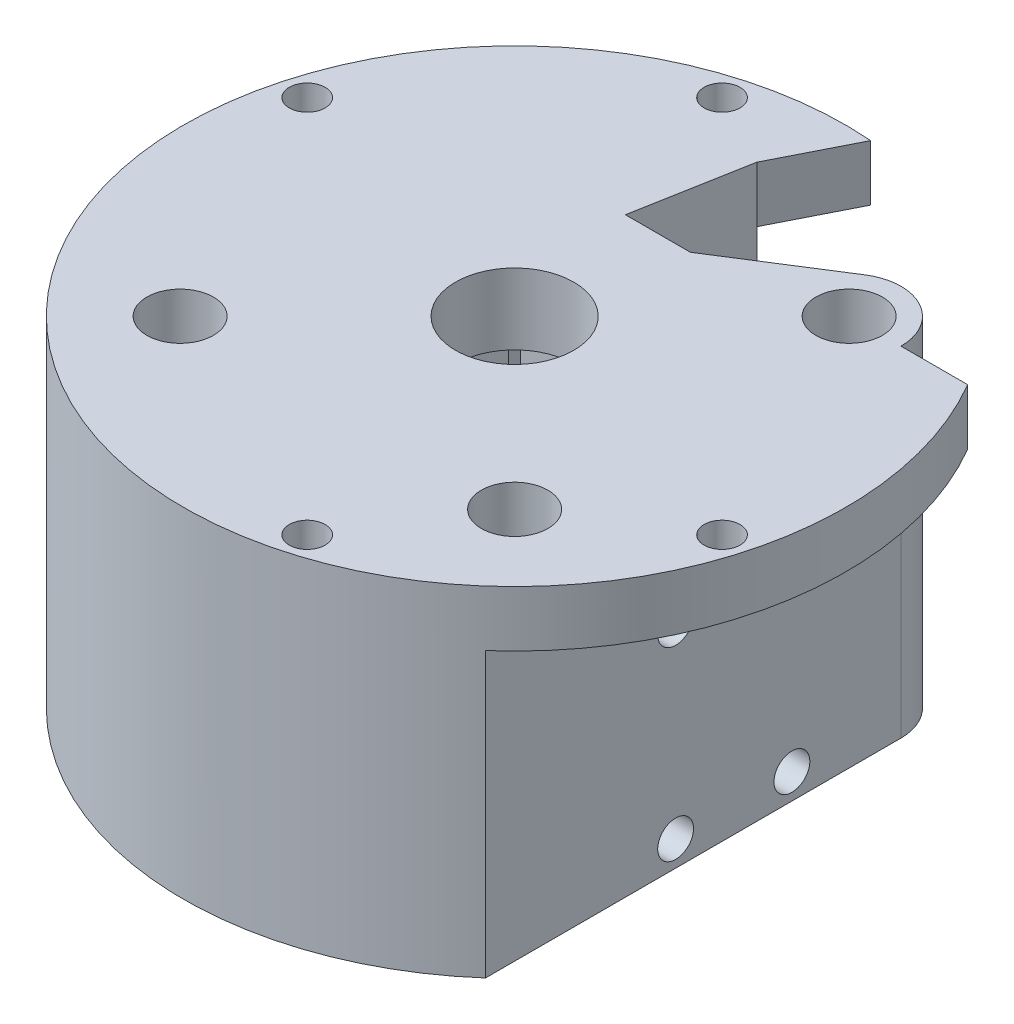
SolidWorks part; units mm, degrees
ref_plane "Front Plane" through (0, 0, 0) normal (0, 0, 1) x (1, 0, 0)
ref_plane "Top Plane" through (0, 0, 0) normal (0, 1, 0) x (1, 0, 0)
ref_plane "Right Plane" through (0, 0, 0) normal (1, 0, 0) x (0, 0, -1)
sketch "Sketch2" plane through (0, 0, 0) normal (0, 1, 0) x (1, 0, 0)
  line L0 (-46.3406, 15.0473) -> (-20.9548, -39.0545) construction
  line L1 (-17.9605, 17.9605) -> (-3.0236, 17.9605) construction
  line L2 (-17.9605, 17.9605) -> (-17.9605, -17.9605) construction
  line L3 (-17.9605, -17.9605) -> (17.9605, -17.9605) construction
  line L4 (17.9605, 17.9605) -> (17.9605, -17.9605) construction
  line L5 (-17.9605, 17.9605) -> (17.9605, -17.9605) construction
  line L6 (-17.9605, -17.9605) -> (17.9605, 17.9605) construction
  line L7 (10.05, -30.05) -> (-10.05, -30.05)
  line L8 (10.05, -30.05) -> (10.05, 10.05)
  line L9 (10.05, 10.05) -> (3.4925, 10.05)
  line L10 (-10.05, -30.05) -> (-10.05, 10.05)
  line L11 (10.05, -30.05) -> (-10.05, 10.05) construction
  line L12 (10.05, 10.05) -> (-10.05, -30.05) construction
  line L13 (-3.4925, 15.384) -> (3.4925, 15.384) construction
  line L14 (-3.4925, 15.384) -> (-3.4925, 10.05)
  line L15 (0, 10.05) -> (3.4925, 10.05) construction
  line L16 (3.4925, 15.384) -> (3.4925, 10.05)
  line L17 (0, 12.717) -> (3.4925, 10.05) construction
  line L18 (0, 12.717) -> (3.4925, 15.384) construction
  line L19 (-1.3182, 27.3309) -> (-10.8398, 32.142)
  line L20 (-1.3182, 27.3309) -> (-23.3118, -16.1961) construction
  line L21 (-23.3118, -16.1961) -> (-32.8333, -11.3851) construction
  line L22 (-10.8398, 32.142) -> (-32.8333, -11.3851) construction
  line L23 (-1.3182, 27.3309) -> (-32.8333, -11.3851) construction
  line L24 (-23.3118, -16.1961) -> (-10.8398, 32.142) construction
  line L25 (23.5324, -17.9605) -> (23.5324, -26.6597)
  line L26 (23.5324, -17.9605) -> (23.5324, 17.9605)
  line L27 (3.4925, 15.384) -> (14.9767, 22.6661)
  line L28 (-10.8398, 32.142) -> (-12.8493, 33.1573)
  line L29 (-3.4925, 15.384) -> (-1.3182, 27.3309)
  line L30 (-3.0236, 17.9605) -> (7.5558, 17.9605) construction
  line L31 (7.5558, 17.9605) -> (17.9605, 17.9605) construction
  line L32 (-3.4925, 15.384) -> (0, 12.717) construction
  line L33 (-3.4925, 10.05) -> (0, 12.717) construction
  line L34 (0, 10.05) -> (-3.4925, 10.05) construction
  line L35 (-3.4925, 10.05) -> (-10.05, 10.05)
  line L36 (-3.4925, 10.05) -> (0, 10.05) construction
  line L37 (3.4925, 10.05) -> (0, 10.05) construction
  arc A0 (-12.8493, 33.1573) -> (23.5324, -26.6597) centre (0, 0) ccw
  circle A1 centre (-17.9605, 17.9605) radius 3.5719 construction
  circle A2 centre (17.9605, 17.9605) radius 3.5719
  circle A3 centre (17.9605, -17.9605) radius 3.5719
  circle A4 centre (-17.9605, -17.9605) radius 3.5719
  arc A5 (-4.4901, 4.4901) -> (4.4901, 4.4901) centre (0, 0) ccw construction
  arc A6 (-7.1064, 7.1064) -> (7.1064, 7.1064) centre (0, 0) ccw construction
  circle A7 centre (-17.9605, -17.9605) radius 5.5719 construction
  arc A8 (23.5324, -17.9605) -> (17.9605, -12.3886) centre (17.9605, -17.9605) ccw construction
  arc A9 (23.5324, 17.9605) -> (14.9767, 22.6661) centre (17.9605, 17.9605) ccw
  arc A10 (23.5324, -26.6597) -> (-12.8493, 33.1573) centre (0, 0) ccw construction
  arc A11 (0, 10.05) -> (-7.1064, 7.1064) centre (0, 0) ccw construction
  arc A12 (4.4901, 4.4901) -> (-4.4901, 4.4901) centre (0, 0) ccw construction
  arc A13 (7.1064, 7.1064) -> (0, 10.05) centre (0, 0) ccw construction
  arc A14 (14.0206, 14.0206) -> (17.9605, 12.3886) centre (17.9605, 17.9605) ccw construction
  arc A15 (12.3886, 17.9605) -> (14.0206, 14.0206) centre (17.9605, 17.9605) ccw construction
  arc A16 (14.9767, 22.6661) -> (12.3886, 17.9605) centre (17.9605, 17.9605) ccw construction
  arc A17 (17.9605, 12.3886) -> (23.5324, 17.9605) centre (17.9605, 17.9605) ccw construction
  arc A18 (12.3886, -17.9605) -> (23.5324, -17.9605) centre (17.9605, -17.9605) ccw construction
  arc A19 (14.0206, -14.0206) -> (12.3886, -17.9605) centre (17.9605, -17.9605) ccw construction
  arc A20 (17.9605, -12.3886) -> (14.0206, -14.0206) centre (17.9605, -17.9605) ccw construction
  point P12 (0, -10)
  point P17 (0, 12.717)
  point P23 (-17.0758, 7.9729)
  point P35 (-32.1922, -15.1054)
  dimension "D1" = 71.12
  dimension "D3" = 7.1437
  dimension "D4" = 12.7
  dimension "D2" = 50.8
  dimension "D5" = 20.1
  dimension "D6" = 40.1
  dimension "D7" = 10
  dimension "D8" = 6.985
  dimension "D9" = 5.334
  dimension "D10" = 10.668
  dimension "D11" = 48.768
  dimension "D12" = 10.668
  dimension "D13" = 2
  dimension "D14" = 1
  dimension "D15" = 38.056
extrude "Boss-Extrude1" add sketch "Sketch2" along normal blind 1.905
sketch "Sketch3" plane through (0, 1.905, 0) normal (0, 1, 0) x (1, 0, 0)
  line L0 (-1.3182, 27.3309) -> (-23.3118, -16.1961) construction
  line L1 (-10.8398, 32.142) -> (-32.8333, -11.3851) construction
  line L2 (-23.3118, -16.1961) -> (-32.8333, -11.3851) construction
  line L3 (-10.8398, 32.142) -> (-32.8333, -11.3851)
  line L4 (-1.3182, 27.3309) -> (-9.7636, 10.6168)
  line L5 (-23.3118, -16.1961) -> (-32.8333, -11.3851)
  line L6 (-10.05, 10.05) -> (-9.415, 10.05) construction
  line L7 (-9.7636, 10.6168) -> (-10.05, 10.05) construction
  line L8 (-10.3364, 9.4832) -> (-23.3118, -16.1961)
  line L9 (-10.05, 10.05) -> (-10.3364, 9.4832) construction
  line L10 (-10.05, 9.415) -> (-10.05, 10.05) construction
  line L11 (-10.05, 10.05) -> (-3.4925, 10.05)
  line L12 (-3.4925, 10.05) -> (-3.4925, 15.384)
  line L13 (-3.4925, 15.384) -> (-1.3182, 27.3309)
  line L14 (-1.3182, 27.3309) -> (-12.8493, 33.1573)
  line L15 (23.5324, -26.6597) -> (23.5324, 17.9605)
  line L16 (14.9767, 22.6661) -> (3.4925, 15.384)
  line L17 (3.4925, 15.384) -> (3.4925, 10.05)
  line L18 (3.4925, 10.05) -> (10.05, 10.05)
  line L19 (10.05, 10.05) -> (10.05, -30.05)
  line L20 (10.05, -30.05) -> (-10.05, -30.05)
  line L21 (-10.05, -30.05) -> (-10.05, 10.05)
  line L22 (-9.415, 10.05) -> (-3.4925, 10.05)
  line L23 (-3.4925, 10.05) -> (-3.4925, 15.384)
  line L24 (-3.4925, 15.384) -> (-1.3182, 27.3309)
  line L25 (-10.8398, 32.142) -> (-12.8493, 33.1573)
  line L26 (23.5324, -26.6597) -> (23.5324, 17.9605)
  line L27 (14.9767, 22.6661) -> (3.4925, 15.384)
  line L28 (3.4925, 15.384) -> (3.4925, 10.05)
  line L29 (3.4925, 10.05) -> (10.05, 10.05)
  line L30 (10.05, 10.05) -> (10.05, -30.05)
  line L31 (10.05, -30.05) -> (-10.05, -30.05)
  line L32 (-10.05, -30.05) -> (-10.05, 9.415)
  line L33 (-1.3182, 27.3309) -> (-10.8398, 32.142) construction
  arc A0 (-10.3364, 9.4832) -> (-10.05, 9.415) centre (-10.05, 10.05) ccw
  circle A1 centre (17.9605, 17.9605) radius 3.5719 construction
  circle A2 centre (17.9605, -17.9605) radius 3.5719 construction
  arc A3 (-12.8493, 33.1573) -> (23.5324, -26.6597) centre (0, 0) ccw
  arc A4 (23.5324, 17.9605) -> (14.9767, 22.6661) centre (17.9605, 17.9605) ccw
  arc A5 (-12.8493, 33.1573) -> (23.5324, -26.6597) centre (0, 0) ccw
  arc A6 (23.5324, 17.9605) -> (14.9767, 22.6661) centre (17.9605, 17.9605) ccw
  circle A7 centre (-17.9605, -17.9605) radius 3.5719 construction
  circle A8 centre (17.9605, 17.9605) radius 3.5719
  circle A9 centre (17.9605, -17.9605) radius 3.5719
  circle A10 centre (-17.9605, -17.9605) radius 3.5719
  arc A11 (-9.7636, 10.6168) -> (-10.3364, 9.4832) centre (-10.05, 10.05) ccw construction
  arc A12 (-10.05, 9.415) -> (-9.415, 10.05) centre (-10.05, 10.05) ccw construction
  arc A13 (-9.415, 10.05) -> (-9.7636, 10.6168) centre (-10.05, 10.05) ccw
  dimension "D1" = 1.27
  dimension "D2" = 0
extrude "Boss-Extrude2" add sketch "Sketch3" along normal blind 19.558
sketch "Sketch4" plane through (0, 21.463, 0) normal (0, 1, 0) x (1, 0, 0)
  line L0 (0, 10.05) -> (3.4925, 10.05) construction
  line L1 (-3.4925, 15.384) -> (3.4925, 15.384) construction
  line L2 (0, 10.05) -> (-3.4925, 10.05) construction
  line L3 (0, 10.05) -> (-3.4925, 10.05)
  line L4 (0, 10.05) -> (3.4925, 10.05)
  line L5 (-3.4925, 15.384) -> (3.4925, 15.384)
  line L6 (-23.3118, -16.1961) -> (-32.8333, -11.3851) construction
  line L7 (-10.8398, 32.142) -> (-32.8333, -11.3851) construction
  line L8 (-1.3182, 27.3309) -> (-23.3118, -16.1961) construction
  line L9 (-23.3118, -16.1961) -> (-32.8333, -11.3851)
  line L10 (-10.8398, 32.142) -> (-32.8333, -11.3851)
  line L11 (-10.05, 10.05) -> (-3.4925, 10.05)
  line L12 (-10.05, -30.05) -> (-10.05, 10.05)
  line L13 (10.05, -30.05) -> (-10.05, -30.05)
  line L14 (10.05, 10.05) -> (10.05, -30.05)
  line L15 (3.4925, 10.05) -> (10.05, 10.05)
  line L16 (3.4925, 15.384) -> (3.4925, 10.05)
  line L17 (14.9767, 22.6661) -> (3.4925, 15.384)
  line L18 (23.5324, -26.6597) -> (23.5324, 17.9605)
  line L19 (-1.3182, 27.3309) -> (-12.8493, 33.1573)
  line L20 (-3.4925, 15.384) -> (-1.3182, 27.3309)
  line L21 (-3.4925, 10.05) -> (-3.4925, 15.384)
  line L22 (-9.415, 10.05) -> (-3.4925, 10.05)
  line L23 (-10.05, -30.05) -> (-10.05, 9.415)
  line L24 (10.05, -30.05) -> (-10.05, -30.05)
  line L25 (10.05, 10.05) -> (10.05, -30.05)
  line L26 (3.4925, 10.05) -> (10.05, 10.05)
  line L27 (3.4925, 15.384) -> (3.4925, 10.05) construction
  line L28 (14.9767, 22.6661) -> (3.4925, 15.384)
  line L29 (23.5324, -26.6597) -> (23.5324, 17.9605)
  line L30 (-10.8398, 32.142) -> (-12.8493, 33.1573)
  line L31 (-3.4925, 15.384) -> (-1.3182, 27.3309)
  line L32 (-3.4925, 10.05) -> (-3.4925, 15.384) construction
  line L33 (-1.3182, 27.3309) -> (-9.7636, 10.6168)
  line L34 (-1.3182, 27.3309) -> (-10.8398, 32.142) construction
  line L35 (-10.05, 10.05) -> (-10.3364, 9.4832) construction
  line L36 (-10.3364, 9.4832) -> (-23.3118, -16.1961)
  line L37 (-10.05, 9.415) -> (-10.05, 10.05) construction
  line L38 (-10.05, 10.05) -> (-9.415, 10.05) construction
  line L39 (-9.7636, 10.6168) -> (-10.05, 10.05) construction
  circle A0 centre (17.9605, 17.9605) radius 3.5719 construction
  circle A1 centre (17.9605, -17.9605) radius 3.5719 construction
  arc A2 (23.5324, 17.9605) -> (14.9767, 22.6661) centre (17.9605, 17.9605) ccw
  arc A3 (-12.8493, 33.1573) -> (23.5324, -26.6597) centre (0, 0) ccw
  arc A4 (23.5324, 17.9605) -> (14.9767, 22.6661) centre (17.9605, 17.9605) ccw
  arc A5 (-12.8493, 33.1573) -> (23.5324, -26.6597) centre (0, 0) ccw
  circle A6 centre (-17.9605, -17.9605) radius 3.5719 construction
  circle A7 centre (17.9605, 17.9605) radius 3.5719
  circle A8 centre (17.9605, -17.9605) radius 3.5719
  circle A9 centre (-17.9605, -17.9605) radius 3.5719
  arc A10 (-9.415, 10.05) -> (-9.7636, 10.6168) centre (-10.05, 10.05) ccw construction
  arc A11 (-10.3364, 9.4832) -> (-10.05, 9.415) centre (-10.05, 10.05) ccw construction
  arc A12 (-9.415, 10.05) -> (-9.7636, 10.6168) centre (-10.05, 10.05) ccw
  arc A13 (-10.3364, 9.4832) -> (-10.05, 9.415) centre (-10.05, 10.05) ccw
  dimension "D1" = 0
extrude "Boss-Extrude3" add sketch "Sketch4" along normal blind 7.366
sketch "Sketch5" plane through (0, 28.829, 0) normal (0, 1, 0) x (1, 0, 0)
  line L0 (3.4925, 15.384) -> (-3.4925, 15.384) construction
  line L1 (3.4925, 15.384) -> (-3.4925, 15.384)
  line L11 (-10.05, 10.05) -> (-3.4925, 10.05)
  line L12 (-10.05, -30.05) -> (-10.05, 10.05)
  line L13 (10.05, -30.05) -> (-10.05, -30.05)
  line L14 (10.05, 10.05) -> (10.05, -30.05)
  line L15 (3.4925, 10.05) -> (10.05, 10.05)
  line L16 (3.4925, 15.384) -> (3.4925, 10.05)
  line L17 (14.9767, 22.6661) -> (3.4925, 15.384)
  line L18 (23.5324, -26.6597) -> (23.5324, 17.9605)
  line L19 (-1.3182, 27.3309) -> (-12.8493, 33.1573)
  line L20 (-3.4925, 15.384) -> (-1.3182, 27.3309)
  line L21 (-3.4925, 10.05) -> (-3.4925, 15.384)
  line L22 (-10.05, 10.05) -> (-3.4925, 10.05) construction
  line L23 (-10.05, -30.05) -> (-10.05, 10.05) construction
  line L24 (10.05, -30.05) -> (-10.05, -30.05) construction
  line L25 (10.05, 10.05) -> (10.05, -30.05) construction
  line L26 (3.4925, 10.05) -> (10.05, 10.05) construction
  line L27 (3.4925, 15.384) -> (3.4925, 10.05) construction
  line L28 (14.9767, 22.6661) -> (3.4925, 15.384)
  line L29 (23.5324, -26.6597) -> (23.5324, 17.9605)
  line L30 (-1.3182, 27.3309) -> (-12.8493, 33.1573)
  line L31 (-3.4925, 15.384) -> (-1.3182, 27.3309)
  line L32 (-3.4925, 10.05) -> (-3.4925, 15.384) construction
  circle A0 centre (17.9605, 17.9605) radius 3.5719 construction
  circle A1 centre (17.9605, -17.9605) radius 3.5719 construction
  arc A2 (23.5324, 17.9605) -> (14.9767, 22.6661) centre (17.9605, 17.9605) ccw
  arc A3 (-12.8493, 33.1573) -> (23.5324, -26.6597) centre (0, 0) ccw
  arc A4 (23.5324, 17.9605) -> (14.9767, 22.6661) centre (17.9605, 17.9605) ccw
  arc A5 (-12.8493, 33.1573) -> (23.5324, -26.6597) centre (0, 0) ccw
  circle A6 centre (-17.9605, -17.9605) radius 3.5719 construction
  circle A7 centre (17.9605, 17.9605) radius 3.5719
  circle A8 centre (17.9605, -17.9605) radius 3.5719
  circle A9 centre (-17.9605, -17.9605) radius 3.5719
  arc A10 (4.4901, 4.4901) -> (-4.4901, 4.4901) centre (0, 0) ccw construction
  arc A11 (-4.4901, 4.4901) -> (4.4901, 4.4901) centre (0, 0) ccw construction
  arc A12 (4.4901, 4.4901) -> (-4.4901, 4.4901) centre (0, 0) ccw
  arc A13 (-4.4901, 4.4901) -> (4.4901, 4.4901) centre (0, 0) ccw
  dimension "D1" = 0
extrude "Boss-Extrude4" add sketch "Sketch5" along normal blind 7.62
sketch "Sketch6" plane through (23.5324, 0, 0) normal (1, 0, 0) x (0, 0, -1)
  line L0 (32.142, 0) -> (-11.3851, 0) construction
  line L1 (-6.243, 22.6577) -> (6.243, 22.6577) construction
  line L2 (-6.243, 22.6577) -> (-6.243, 2.7422) construction
  line L3 (-6.243, 2.7422) -> (6.243, 2.7422) construction
  line L4 (6.243, 22.6577) -> (6.243, 2.7422) construction
  line L5 (-6.243, 22.6577) -> (6.243, 2.7422) construction
  line L6 (-6.243, 2.7422) -> (6.243, 22.6577) construction
  circle A0 centre (-6.243, 22.6577) radius 1.925
  circle A1 centre (6.243, 22.6577) radius 1.925
  circle A2 centre (6.243, 2.7422) radius 1.925
  circle A3 centre (-6.243, 2.7422) radius 1.925
  point P0 (0, 12.7)
  dimension "D3" = 3.85
  dimension "D1" = 19.9155
  dimension "D2" = 12.486
  dimension "D4" = 12.7
extrude "Cut-Extrude1" cut sketch "Sketch6" against normal blind 5.75
sketch "Sketch8" plane through (0, 36.449, 0) normal (0, 1, 0) x (1, 0, 0)
  line L0 (-1.3182, 27.3309) -> (-12.8493, 33.1573)
  line L1 (-1.3182, 27.3309) -> (2.7846, 35.4508)
  line L2 (23.5324, 17.9605) -> (30.6909, 17.9605)
  line L3 (23.5324, -17.9605) -> (23.5324, 17.9605) construction
  line L4 (23.5324, -17.9605) -> (23.5324, 17.9605)
  line L5 (23.5324, -17.9605) -> (23.5324, -26.6597) construction
  line L6 (23.5324, -17.9605) -> (23.5324, -26.6597)
  arc A0 (23.5324, -26.6597) -> (-12.8493, 33.1573) centre (0, 0) ccw construction
  arc A1 (23.5324, -26.6597) -> (30.6909, 17.9605) centre (0, 0) ccw
  arc A2 (30.6909, 17.9605) -> (2.7846, 35.4508) centre (0, 0) ccw construction
  arc A3 (2.7846, 35.4508) -> (-12.8493, 33.1573) centre (0, 0) ccw
  point P9 (30.385, 18.4733)
extrude "Boss-Extrude5" add sketch "Sketch8" against normal blind 6
sketch "Sketch7" plane through (0, 36.449, 0) normal (0, 1, 0) x (1, 0, 0)
  line L0 (-31.4663, 9.1924) -> (-9.1924, 31.4663) construction
  line L1 (-9.1924, 31.4663) -> (31.4663, -9.1924) construction
  line L2 (31.4663, -9.1924) -> (9.1924, -31.4663) construction
  line L3 (9.1924, -31.4663) -> (-31.4663, 9.1924) construction
  line L4 (-17.9605, -17.9605) -> (17.9605, 17.9605) construction
  line L5 (-31.4663, 9.1924) -> (31.4663, -9.1924) construction
  line L6 (9.1924, -31.4663) -> (-9.1924, 31.4663) construction
  circle A0 centre (-31.4663, 9.1924) radius 1.925
  circle A1 centre (-9.1924, 31.4663) radius 1.925
  circle A2 centre (31.4663, -9.1924) radius 1.925
  circle A3 centre (9.1924, -31.4663) radius 1.925
  point P6 (0, 0)
  dimension "D3" = 3.85
  dimension "D1" = 57.5
  dimension "D2" = 31.5
extrude "Cut-Extrude2" cut sketch "Sketch7" against normal blind 5.75
equation "\"AIRFRAME_OD\"= 3.142in"
equation "\"AIRFRAME_ID\"= 3.00in"
equation "\"FLAT_T\"= 0.125in"
equation "\"NOSE_EXP_L\"= 3.5in"
equation "\"NOSE_SHOULDER_L\"= 1.5in"
equation "\"MAIN_L\"= 30in"
equation "\"RECO_COUP_L\"= 6in"
equation "\"RECO_SWITCH_L\"= 1.5in"
equation "\"DROGUE_L\"= 14in"
equation "\"ATS_FORE_COUP_L\"= 4in"
equation "\"ATS_AFT_COUP_L\"= 2.5in"
equation "\"LOWER_L\"= 16in"
equation "\"FIN_N\"= 4"
equation "\"CR_AFT_X\"= 0.5in"
equation "\"CR_FORE_X\"= 6in"
equation "\"COUPLER_OD\"= 2.998in"
equation "\"COUPLER_ID\"= 2.875in"
equation "\"RECO_ROD_X\"= 1.5in"
equation "\"ATS_ROD_X\"= 2in"
equation "\"FIN_ROOT\"= 5in"
equation "\"FIN_X\"= 0.75in"
equation "\"MOTOR_OD\"= 2.25in"
equation "\"MOTOR_ID\"= 2.126in"
equation "\"MOTOR_L\"= 8in"
equation "\"MOTOR_LOWER_X\"= 0.5in"
equation "\"NOSE_CONE_L\"=14.5in"
equation "\"ATS_LIPO_L\" = 1.92in"
equation "\"ATS_LIPO_W\" = 0.42in"
equation "\"ATS_LIPO_H\" = 0.94in "
equation "\"ATS_STANDOFF_H\" = 10mm"
equation "\"ATS_STANDOFF_OD\" = 5.2mm"
equation "\"ATS_PCB_L\" = 2.5in"
equation "\"ATS_PCB_W\" = 1.45in"
equation "\"ATS_PCB_H\" = 1.2in"
equation "\"ATS_PCB_HOLESEP_W\" = 1.33in - 0.0985in"
equation "\"ATS_ALTI_L\" = 1.05in"
equation "\"ATS_ALTI_W\" = 0.7in"
equation "\"ATS_ALTI_H\" = 0.4in"
equation "\"D11@Sketch2\"=\"ATS_LIPO_L\""
equation "\"D12@Sketch2\"=\"ATS_LIPO_W\""
equation "\"D1@Boss-Extrude2\"=\"ATS_LIPO_H\""
